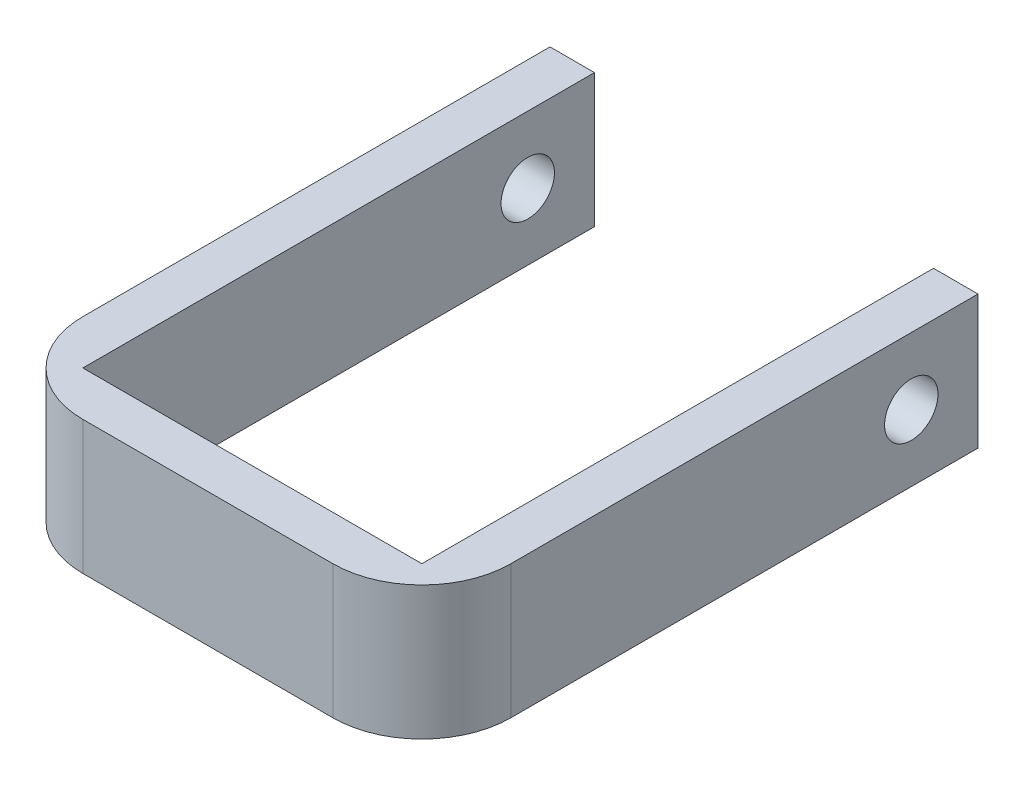
SolidWorks part; units mm, degrees
ref_plane "Front Plane" through (0, 0, 0) normal (0, 0, 1) x (1, 0, 0)
ref_plane "Top Plane" through (0, 0, 0) normal (0, 1, 0) x (1, 0, 0)
ref_plane "Right Plane" through (0, 0, 0) normal (1, 0, 0) x (0, 0, -1)
sketch "Sketch1" plane through (0, 0, 0) normal (0, 1, 0) x (1, 0, 0)
  line L0 (0, 115) -> (-10, 115)
  line L1 (0, 0) -> (76.2, 0)
  line L2 (0, 0) -> (0, 115)
  line L4 (76.2, 0) -> (76.2, 115)
  line L5 (-10, 115) -> (-10, -10)
  line L6 (-10, -10) -> (86.2, -10)
  line L7 (86.2, -10) -> (86.2, 115)
  line L8 (86.2, 115) -> (76.2, 115)
  dimension "D1" = 76.2
  dimension "D2" = 115
  dimension "D3" = 10
  dimension "D4" = 10
  dimension "D5" = 10
  dimension "D6" = 115
extrude "Boss-Extrude1" add sketch "Sketch1" along normal blind 30
fillet "Fillet1" radius 20 2 edges at (86.2, 15, 10) (-10, 15, 10)
sketch "Sketch2" plane through (86.2, 0, 0) normal (1, 0, 0) x (0, 0, -1)
  line L0 (115, 30) -> (115, 0) construction
  circle A0 centre (100, 15) radius 6
  dimension "D1" = 12
  dimension "D2" = 15
extrude "Cut-Extrude1" cut sketch "Sketch2" against normal through all
